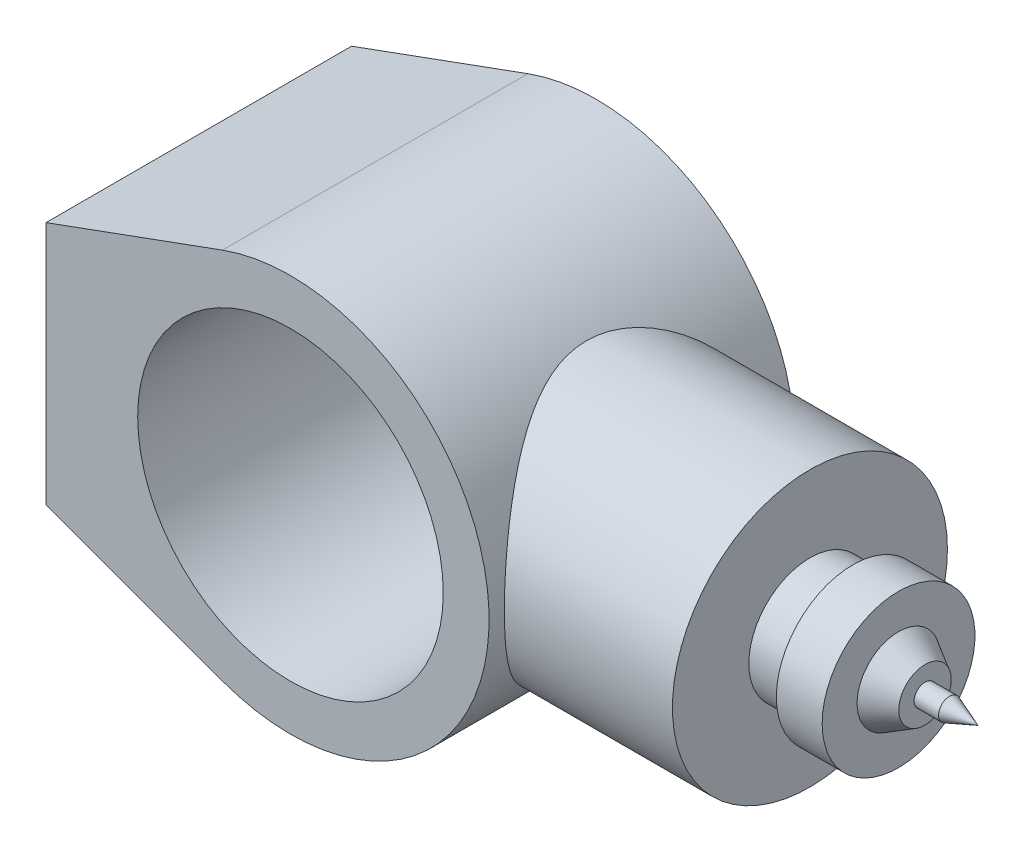
SolidWorks part; units mm, degrees
ref_plane "Front Plane" through (0, 0, 0) normal (0, 0, 1) x (1, 0, 0)
ref_plane "Top Plane" through (0, 0, 0) normal (0, 1, 0) x (1, 0, 0)
ref_plane "Right Plane" through (0, 0, 0) normal (1, 0, 0) x (0, 0, -1)
sketch "Sketch1" plane through (0, 0, 0) normal (0, 0, 1) x (1, 0, 0)
  line L0 (-80, -40) -> (-80, 40)
  line L1 (-80, 40) -> (-22.2817, 61.0617)
  line L2 (-80, -40) -> (-22.2817, -61.0617)
  arc A0 (-22.2817, -61.0617) -> (-22.2817, 61.0617) centre (0, 0) ccw
  circle A1 centre (0, 0) radius 50
  point P7 (-80, 0)
  dimension "D1" = 130
  dimension "D2" = 100
  dimension "D3" = 80
  dimension "D4" = 80
extrude "Boss-Extrude1" add sketch "Sketch1" along normal mid plane 100
ref_plane "Plane1" through (120, 0, 0) normal (1, 0, 0) x (0, 0, -1)
sketch "Sketch2" plane through (120, 0, 0) normal (1, 0, 0) x (0, 0, -1)
  circle A0 centre (0, 0) radius 45
  dimension "D1" = 90
extrude "Boss-Extrude2" add sketch "Sketch2" against normal up to next contours A0
sketch "Sketch5" plane through (0, 0, 0) normal (0, 0, 1) x (1, 0, 0)
  line L0 (0, 0) -> (210.4451, 0) construction
  line L1 (120, 0) -> (120, -20)
  line L2 (120, -45) -> (120, 45) construction
  line L3 (120, -20) -> (134, -20)
  line L4 (134, -20) -> (134, -25)
  line L5 (134, -25) -> (149, -25)
  line L6 (149, -25) -> (149, -13.5734)
  line L7 (149, -13.5734) -> (157.6603, -8.5734)
  line L8 (157.6603, -8.5734) -> (157.6603, -3.5734)
  line L9 (157.6603, -3.5734) -> (165.6603, -3.5734)
  line L10 (165.6603, -3.5734) -> (175, 0)
  line L11 (175, 0) -> (120, 0)
  dimension "D1" = 20
  dimension "D2" = 14
  dimension "D3" = 5
  dimension "D4" = 15
  dimension "D5" = 10
  dimension "D6" = 8
  dimension "D7" = 10
  dimension "D8" = 120
  dimension "D9" = 5
  dimension "D10" = 55
revolve "Revolve1" add sketch "Sketch5" angle 360 about L0
